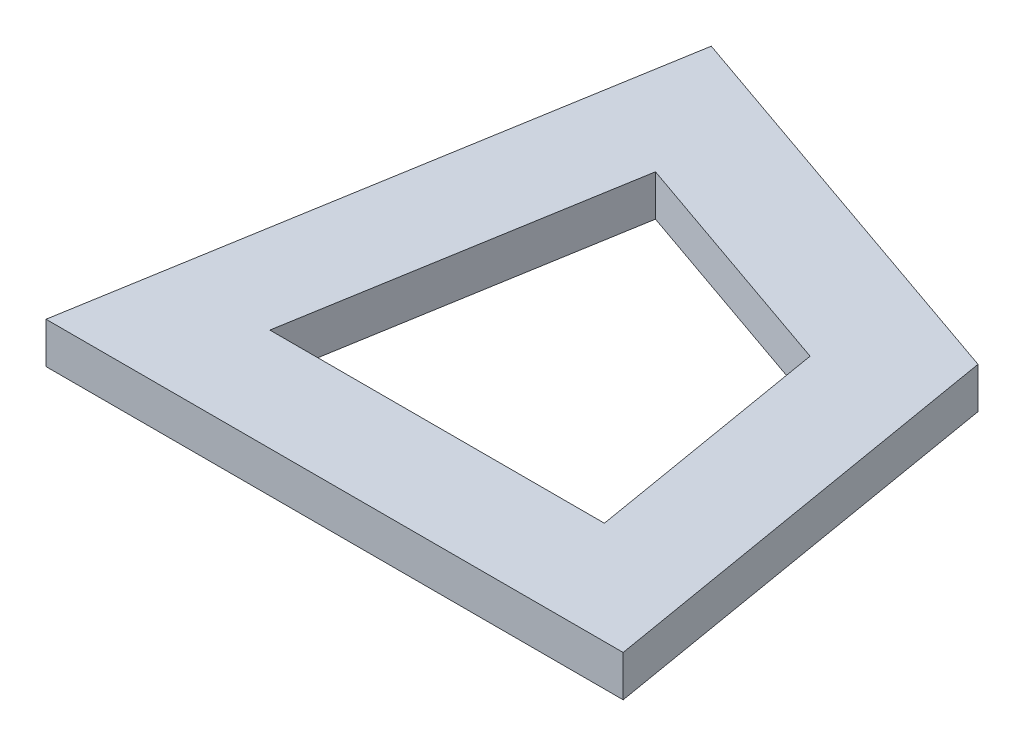
SolidWorks part; units mm, degrees
ref_plane "Front Plane" through (0, 0, 0) normal (0, 0, 1) x (1, 0, 0)
ref_plane "Top Plane" through (0, 0, 0) normal (0, 1, 0) x (1, 0, 0)
ref_plane "Right Plane" through (0, 0, 0) normal (1, 0, 0) x (0, 0, -1)
sketch "Sketch1" plane through (0, 0, 0) normal (0, 1, 0) x (1, 0, 0)
  line L0 (0, 0) -> (28.1432, 0)
  line L1 (28.1432, 0) -> (24.6256, 20.8191)
  line L2 (24.6256, 20.8191) -> (4.6886, 27.7499)
  line L3 (4.6886, 27.7499) -> (0, 0)
  line L4 (8.6333, 21.0851) -> (5.9157, 5)
  line L5 (5.9157, 5) -> (22.2275, 5)
  line L6 (22.2275, 5) -> (20.1885, 17.0681)
  line L7 (20.1885, 17.0681) -> (8.6333, 21.0851)
  point P4 (0, 0)
  point P10 (35.273, 13.2401)
  point P11 (27.7587, 61.9651)
  point P12 (35.2745, 13.2436)
  point P13 (30.6569, 10.5612)
  point P14 (35.2745, 13.2436)
  point P15 (32.8598, 27.5353)
  dimension "D1" = 28.1432
  dimension "D2" = 80.421
  dimension "D3" = 80.41
  dimension "D4" = 80.41
  dimension "D6" = 21.1142
  dimension "D7" = 21.1074
  dimension "D8" = 28.1432
  dimension "D5" = 5
extrude "Boss-Extrude1" add sketch "Sketch1" along normal blind 2
